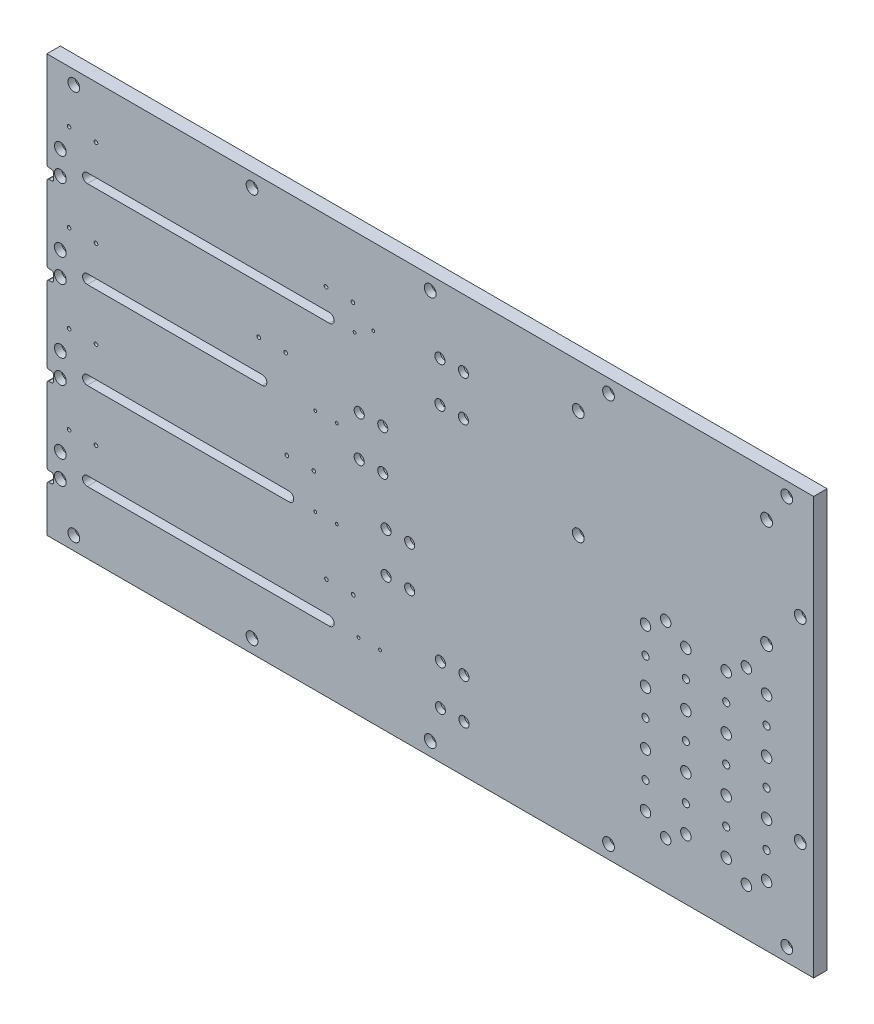
SolidWorks part; units mm, degrees
ref_plane "Front Plane" through (0, 0, 0) normal (0, 0, 1) x (1, 0, 0)
ref_plane "Top Plane" through (0, 0, 0) normal (0, 1, 0) x (1, 0, 0)
ref_plane "Right Plane" through (0, 0, 0) normal (1, 0, 0) x (0, 0, -1)
sketch "Sketch1" plane through (0, 0, 0) normal (0, 0, 1) x (1, 0, 0)
  line L1 (0, 0) -> (723.9, 0)
  line L2 (0, 0) -> (0, -393.7)
  line L3 (0, -393.7) -> (723.9, -393.7)
  line L4 (723.9, 0) -> (723.9, -393.7)
  dimension "D1" = 393.7
  dimension "D2" = 723.9
extrude "Boss-Extrude1" add sketch "Sketch1" against normal blind 12.7
sketch "Sketch2" plane through (0, 0, 0) normal (0, 0, 1) x (1, 0, 0)
  line L0 (38.1, -82.55) -> (266.7, -82.55) construction
  line L1 (38.1, -78.105) -> (266.7, -78.105)
  line L2 (38.1, -86.995) -> (266.7, -86.995)
  line L3 (0, 0) -> (0, -393.7) construction
  line L4 (38.1, -165.1) -> (203.2, -165.1) construction
  line L5 (38.1, -160.655) -> (203.2, -160.655)
  line L6 (38.1, -169.545) -> (203.2, -169.545)
  line L7 (38.1, -247.65) -> (228.6, -247.65) construction
  line L8 (38.1, -243.205) -> (228.6, -243.205)
  line L9 (38.1, -252.095) -> (228.6, -252.095)
  line L10 (38.1, -330.2) -> (266.7, -330.2) construction
  line L11 (38.1, -325.755) -> (266.7, -325.755)
  line L12 (38.1, -334.645) -> (266.7, -334.645)
  arc A0 (38.1, -78.105) -> (38.1, -86.995) centre (38.1, -82.55) ccw
  arc A1 (266.7, -86.995) -> (266.7, -78.105) centre (266.7, -82.55) ccw
  arc A2 (38.1, -160.655) -> (38.1, -169.545) centre (38.1, -165.1) ccw
  arc A3 (203.2, -169.545) -> (203.2, -160.655) centre (203.2, -165.1) ccw
  arc A4 (38.1, -243.205) -> (38.1, -252.095) centre (38.1, -247.65) ccw
  arc A5 (228.6, -252.095) -> (228.6, -243.205) centre (228.6, -247.65) ccw
  arc A6 (38.1, -325.755) -> (38.1, -334.645) centre (38.1, -330.2) ccw
  arc A7 (266.7, -334.645) -> (266.7, -325.755) centre (266.7, -330.2) ccw
  point P2 (152.4, -82.55)
  point P12 (120.65, -165.1)
  point P19 (133.35, -247.65)
  point P24 (152.4, -330.2)
  dimension "D16" = 38.1
  dimension "D1" = 8.89
  dimension "D2" = 38.1
  dimension "D3" = 228.6
  dimension "D4" = 82.55
  dimension "D5" = 8.89
  dimension "D6" = 38.1
  dimension "D7" = 82.55
  dimension "D8" = 165.1
  dimension "D9" = 8.89
  dimension "D10" = 190.5
  dimension "D11" = 82.55
  dimension "D12" = 8.89
  dimension "D13" = 38.1
  dimension "D14" = 82.55
  dimension "D15" = 228.6
extrude "Cut-Extrude1" cut sketch "Sketch2" against normal blind 12.7
ref_plane "Plane1" through (0, -82.55, 0) normal (0, -1, 0) x (-1, 0, 0)
sketch "Sketch5" plane through (0, 0, 0) normal (0, 0, 1) x (1, 0, 0)
  line L0 (0, 0) -> (0, -393.7) construction
  line L1 (0, -174.775) -> (6.35, -174.775)
  line L2 (0, -174.775) -> (0, -184.3)
  line L3 (0, -184.3) -> (6.35, -184.3)
  line L4 (6.35, -174.775) -> (6.35, -184.3)
  line L5 (7, -171.6) -> (0, -171.6) construction
  line L6 (7, -89.05) -> (0, -89.05) construction
  line L7 (0, -92.225) -> (6.35, -92.225)
  line L8 (0, -92.225) -> (0, -101.75)
  line L9 (0, -101.75) -> (6.35, -101.75)
  line L10 (6.35, -92.225) -> (6.35, -101.75)
  line L11 (7, -254.15) -> (0, -254.15) construction
  line L12 (0, -257.325) -> (6.35, -257.325)
  line L13 (0, -257.325) -> (0, -266.85)
  line L14 (0, -266.85) -> (6.35, -266.85)
  line L15 (6.35, -257.325) -> (6.35, -266.85)
  line L16 (7, -336.7) -> (0, -336.7) construction
  line L17 (0, -339.875) -> (6.35, -339.875)
  line L18 (0, -339.875) -> (0, -349.4)
  line L19 (0, -349.4) -> (6.35, -349.4)
  line L20 (6.35, -339.875) -> (6.35, -349.4)
  dimension "D1" = 9.525
  dimension "D2" = 6.35
  dimension "D3" = 3.175
  dimension "D4" = 3.175
  dimension "D5" = 9.525
  dimension "D6" = 6.35
  dimension "D7" = 9.525
  dimension "D8" = 3.175
  dimension "D9" = 6.35
  dimension "D10" = 9.525
  dimension "D11" = 3.175
  dimension "D12" = 6.35
extrude "Cut-Extrude2" cut sketch "Sketch5" against normal through all
sketch "Sketch7" plane through (0, 0, -12.7) normal (0, 0, -1) x (-1, 0, 0)
  circle A6 centre (-20.955, -296.9946) radius 2.0193
  circle A7 centre (-46.355, -296.9946) radius 2.0193
  circle A8 centre (-20.955, -214.3125) radius 2.0193
  circle A9 centre (-46.355, -214.3125) radius 2.0193
  circle A10 centre (-20.955, -131.7625) radius 2.0193
  circle A11 centre (-46.355, -131.7625) radius 2.0193
  point P9 (0, 0)
  point P18 (0, 0)
  point P19 (0, 0)
fillet "Fillet1" radius 2.032 16 edges at (6.35, -101.75, -6.35) (0, -101.75, -6.35) (6.35, -92.225, -6.35) (0, -92.225, -6.35) (6.35, -174.775, -6.35) (0, -174.775, -6.35) (6.35, -184.3, -6.35) (0, -184.3, -6.35) (0, -266.85, -6.35) (6.35, -266.85, -6.35) (0, -257.325, -6.35) (6.35, -257.325, -6.35) (0, -349.4, -6.35) (6.35, -349.4, -6.35) (6.35, -339.875, -6.35) (0, -339.875, -6.35)
hole_wizard "#6-32 Tapped Hole1" positions "Sketch8" profile "Sketch9" tap size "#6-32" standard "ANSI Inch" end condition through all
sketch "Sketch8" plane through (0, 0, -12.7) normal (0, 0, -1) x (-1, 0, 0)
  point P0 (-20.955, -131.7625)
  point P3 (-46.355, -131.7625)
  point P6 (-46.355, -214.3125)
  point P9 (-20.955, -214.3125)
  point P12 (-46.355, -296.9946)
  point P15 (-20.955, -296.9946)
sketch "Sketch9" plane through (20.955, -131.7625, -12.7) normal (1, 0, 0) x (0, 1, 0)
  line L0 (0, 0) -> (0, 12.7)
  line L1 (0, 12.7) -> (1.3525, 12.7)
  line L2 (1.3525, 12.7) -> (1.3525, 0)
  line L5 (1.3525, 0) -> (0, 0)
  line L11 (0, -6.35) -> (0, 107.95) construction
  dimension "Thru Tap Drill Dia." = 2.7051
  dimension "Thru Tap Drill Depth" = 12.7
sketch "Sketch10" plane through (0, 0, 0) normal (0, 0, 1) x (1, 0, 0)
  line L0 (723.9, -393.7) -> (723.9, 0) construction
  line L1 (0, -393.7) -> (723.9, -393.7) construction
  line L2 (0, -351.432) -> (0, -393.7) construction
  line L3 (723.9, -196.85) -> (806.2378, -196.85) construction
  point P0 (698.5, -381)
  point P1 (530.225, -381)
  point P2 (361.95, -381)
  point P3 (193.675, -381)
  point P4 (711.2, -196.85)
  point P7 (25.4, -12.7)
  point P8 (193.675, -12.7)
  point P13 (361.95, -12.7)
  point P14 (530.225, -12.7)
  point P15 (25.4, -381)
  point P18 (698.5, -12.7)
  point P19 (711.2, -288.925)
  point P20 (711.2, -104.775)
  dimension "D1" = 25.4
  dimension "D2" = 12.7
  dimension "D3" = 168.275
  dimension "D4" = 168.275
  dimension "D5" = 168.275
  dimension "D6" = 25.4
  dimension "D7" = 92.075
  dimension "D8" = 92.075
  dimension "D9" = 92.075
  dimension "D10" = 12.7
hole_wizard "CBORE for 1/4 Socket Head Cap Screw1" positions "Sketch13" profile "Sketch14" counterbore size "1/4" standard "ANSI Inch" end condition through all
sketch "Sketch13" plane through (0, 0, 0) normal (0, 0, 1) x (1, 0, 0)
  point P0 (25.4, -381)
  point P3 (193.675, -381)
  point P6 (361.95, -381)
  point P9 (530.225, -381)
  point P12 (698.5, -381)
  point P15 (711.2, -288.925)
  point P21 (711.2, -104.775)
  point P24 (698.5, -12.7)
  point P27 (530.225, -12.7)
  point P30 (361.95, -12.7)
  point P33 (193.675, -12.7)
  point P36 (25.4, -12.7)
sketch "Sketch14" plane through (25.4, -381, 0) normal (1, 0, 0) x (0, -1, 0)
  line L0 (0, 0) -> (0, 12.7)
  line L1 (0, 12.7) -> (3.3782, 12.7)
  line L3 (3.3782, 12.7) -> (3.3782, 6.731)
  line L4 (3.3782, 6.731) -> (5.5562, 6.731)
  line L5 (5.5562, 6.731) -> (5.5562, 0)
  line L7 (5.5562, 0) -> (0, 0)
  line L11 (0, -6.35) -> (0, 107.95) construction
  dimension "Thru Hole Dia." = 6.7564
  dimension "Thru Hole Depth" = 12.7
  dimension "C'Bore Dia." = 11.1125
  dimension "C'Bore Depth" = 6.731
sketch "Sketch15" plane through (0, 0, -12.7) normal (0, 0, -1) x (-1, 0, 0)
  circle A0 centre (-565.15, -184.15) radius 3.9687 construction
  circle A1 centre (-565.15, -184.15) radius 3.9687
  circle A2 centre (-565.15, -209.55) radius 3.175 construction
  circle A3 centre (-565.15, -209.55) radius 3.175
  circle A4 centre (-565.15, -209.55) radius 3.3655
  circle A5 centre (-565.15, -184.15) radius 4.953
  circle A6 centre (-679.45, -336.55) radius 3.9688 construction
  circle A7 centre (-660.4, -349.25) radius 3.9687 construction
  circle A8 centre (-641.35, -336.55) radius 3.9688 construction
  circle A9 centre (-641.35, -311.15) radius 3.175 construction
  circle A10 centre (-679.45, -311.15) radius 3.175 construction
  circle A11 centre (-679.45, -285.75) radius 3.9688 construction
  circle A12 centre (-641.35, -285.75) radius 3.9688 construction
  circle A13 centre (-641.35, -260.35) radius 3.175 construction
  circle A14 centre (-679.45, -260.35) radius 3.175 construction
  circle A15 centre (-679.45, -234.95) radius 3.9688 construction
  circle A16 centre (-641.35, -234.95) radius 3.9688 construction
  circle A17 centre (-679.45, -209.55) radius 3.175 construction
  circle A18 centre (-641.35, -209.55) radius 3.175 construction
  circle A19 centre (-679.45, -184.15) radius 3.9688 construction
  circle A20 centre (-660.4, -171.45) radius 3.9687 construction
  circle A21 centre (-641.35, -184.15) radius 3.9688 construction
  circle A22 centre (-584.2, -171.45) radius 3.9687 construction
  circle A23 centre (-603.25, -184.15) radius 3.9687 construction
  circle A24 centre (-603.25, -209.55) radius 3.175 construction
  circle A25 centre (-603.25, -234.95) radius 3.9687 construction
  circle A26 centre (-603.25, -260.35) radius 3.175 construction
  circle A27 centre (-603.25, -285.75) radius 3.9687 construction
  circle A28 centre (-603.25, -311.15) radius 3.175 construction
  circle A29 centre (-603.25, -336.55) radius 3.9687 construction
  circle A30 centre (-584.2, -349.25) radius 3.9687 construction
  circle A31 centre (-565.15, -336.55) radius 3.9687 construction
  circle A32 centre (-565.15, -311.15) radius 3.175 construction
  circle A33 centre (-565.15, -285.75) radius 3.9687 construction
  circle A34 centre (-565.15, -260.35) radius 3.175 construction
  circle A35 centre (-565.15, -234.95) radius 3.9687 construction
  circle A36 centre (-679.45, -336.55) radius 3.9688
  circle A37 centre (-660.4, -349.25) radius 3.9687
  circle A38 centre (-641.35, -336.55) radius 3.9688
  circle A39 centre (-641.35, -311.15) radius 3.175
  circle A40 centre (-679.45, -311.15) radius 3.175
  circle A41 centre (-679.45, -285.75) radius 3.9688
  circle A42 centre (-641.35, -285.75) radius 3.9688
  circle A43 centre (-641.35, -260.35) radius 3.175
  circle A44 centre (-679.45, -260.35) radius 3.175
  circle A45 centre (-679.45, -234.95) radius 3.9688
  circle A46 centre (-641.35, -234.95) radius 3.9688
  circle A47 centre (-679.45, -209.55) radius 3.175
  circle A48 centre (-641.35, -209.55) radius 3.175
  circle A49 centre (-679.45, -184.15) radius 3.9688
  circle A50 centre (-660.4, -171.45) radius 3.9687
  circle A51 centre (-641.35, -184.15) radius 3.9688
  circle A52 centre (-584.2, -171.45) radius 3.9687
  circle A53 centre (-603.25, -184.15) radius 3.9687
  circle A54 centre (-603.25, -209.55) radius 3.175
  circle A55 centre (-603.25, -234.95) radius 3.9687
  circle A56 centre (-603.25, -260.35) radius 3.175
  circle A57 centre (-603.25, -285.75) radius 3.9687
  circle A58 centre (-603.25, -311.15) radius 3.175
  circle A59 centre (-603.25, -336.55) radius 3.9687
  circle A60 centre (-584.2, -349.25) radius 3.9687
  circle A61 centre (-565.15, -336.55) radius 3.9687
  circle A62 centre (-565.15, -311.15) radius 3.175
  circle A63 centre (-565.15, -285.75) radius 3.9687
  circle A64 centre (-565.15, -260.35) radius 3.175
  circle A65 centre (-565.15, -234.95) radius 3.9687
  circle A66 centre (-565.15, -234.95) radius 4.953
  circle A67 centre (-584.2, -171.45) radius 4.953
  circle A68 centre (-603.25, -184.15) radius 4.953
  circle A69 centre (-603.25, -209.55) radius 3.3655
  circle A70 centre (-603.25, -234.95) radius 4.953
  circle A71 centre (-603.25, -260.35) radius 3.3655
  circle A72 centre (-565.15, -260.35) radius 3.3655
  circle A73 centre (-565.15, -285.75) radius 4.7625
  circle A74 centre (-565.15, -311.15) radius 3.3655
  circle A75 centre (-565.15, -336.55) radius 4.953
  circle A76 centre (-584.2, -349.25) radius 4.953
  circle A77 centre (-603.25, -336.55) radius 4.953
  circle A78 centre (-603.25, -311.15) radius 3.3655
  circle A79 centre (-603.25, -285.75) radius 4.953
  circle A80 centre (-641.35, -184.15) radius 4.953
  circle A81 centre (-641.35, -209.55) radius 3.3655
  circle A82 centre (-641.35, -234.95) radius 4.953
  circle A83 centre (-641.35, -260.35) radius 3.3655
  circle A84 centre (-660.4, -171.45) radius 4.953
  circle A85 centre (-679.45, -184.15) radius 4.953
  circle A86 centre (-679.45, -209.55) radius 3.3655
  circle A87 centre (-679.45, -234.95) radius 4.953
  circle A88 centre (-679.45, -260.35) radius 3.3655
  circle A89 centre (-679.45, -285.75) radius 4.953
  circle A90 centre (-641.35, -285.75) radius 4.953
  circle A91 centre (-641.35, -311.15) radius 3.3655
  circle A92 centre (-679.45, -311.15) radius 3.3655
  circle A93 centre (-679.45, -336.55) radius 4.953
  circle A94 centre (-660.4, -349.25) radius 4.953
  circle A95 centre (-641.35, -336.55) radius 4.953
  dimension "D1" = 6.731
  dimension "D2" = 9.906
  dimension "D3" = 9.906
  dimension "D4" = 9.906
  dimension "D5" = 9.906
  dimension "D6" = 6.731
  dimension "D7" = 9.906
  dimension "D8" = 6.731
  dimension "D9" = 6.731
  dimension "D10" = 9.525
  dimension "D11" = 6.731
  dimension "D12" = 9.906
  dimension "D13" = 9.906
  dimension "D14" = 9.906
  dimension "D15" = 6.731
  dimension "D16" = 9.906
  dimension "D17" = 9.906
  dimension "D18" = 6.731
  dimension "D19" = 9.906
  dimension "D20" = 6.731
  dimension "D21" = 9.906
  dimension "D22" = 9.906
  dimension "D23" = 6.731
  dimension "D24" = 9.906
  dimension "D25" = 6.731
  dimension "D26" = 9.906
  dimension "D27" = 9.906
  dimension "D28" = 6.731
  dimension "D29" = 6.731
  dimension "D30" = 9.906
  dimension "D31" = 9.906
  dimension "D32" = 9.906
extrude "Cut-Extrude9" cut sketch "Sketch15" against normal blind 12.7 from surface at 0
ref_plane "Plane2" through (361.95, 0, 0) normal (1, 0, 0) x (0, 0, -1)
ref_plane "Plane3" through (0, -196.85, 0) normal (0, -1, 0) x (-1, 0, 0)
sketch "Sketch16" plane through (0, 0, 0) normal (0, 0, 1) x (1, 0, 0)
  line L1 (-3.175, -396.875) -> (727.075, -396.875)
  line L2 (-3.175, -396.875) -> (-3.175, 3.175)
  line L3 (-3.175, 3.175) -> (727.075, 3.175)
  line L4 (727.075, -396.875) -> (727.075, 3.175)
  line L5 (-3.175, -396.875) -> (727.075, 3.175) construction
  line L6 (-3.175, 3.175) -> (727.075, -396.875) construction
  line L7 (361.95, -6.985) -> (361.95, 6.985) construction
  line L8 (-6.985, -196.85) -> (6.985, -196.85) construction
  point P0 (361.95, -196.85)
  dimension "D1" = 730.25
  dimension "D2" = 400.05
hole_wizard "CBORE for 1/4 Socket Head Cap Screw2" positions "Sketch17" profile "Sketch18" counterbore size "1/4" standard "ANSI Inch" end condition through all
sketch "Sketch17" plane through (0, 0, 0) normal (0, 0, 1) x (1, 0, 0)
  point P0 (12.7, -319.0875)
  point P3 (12.7, -341.3125)
  point P6 (12.7, -258.7625)
  point P9 (12.7, -236.5375)
  point P12 (12.7, -176.2125)
  point P15 (12.7, -153.9875)
  point P18 (12.7, -93.6625)
  point P21 (12.7, -71.4375)
sketch "Sketch18" plane through (12.7, -319.0875, 0) normal (1, 0, 0) x (0, -1, 0)
  line L0 (0, 0) -> (0, 12.7)
  line L1 (0, 12.7) -> (3.3782, 12.7)
  line L3 (3.3782, 12.7) -> (3.3782, 6.731)
  line L4 (3.3782, 6.731) -> (5.5562, 6.731)
  line L5 (5.5562, 6.731) -> (5.5562, 0)
  line L7 (5.5562, 0) -> (0, 0)
  line L11 (0, -6.35) -> (0, 107.95) construction
  dimension "Thru Hole Dia." = 6.7564
  dimension "Thru Hole Depth" = 12.7
  dimension "C'Bore Dia." = 11.1125
  dimension "C'Bore Depth" = 6.731
hole_wizard "#6-32 Tapped Hole2" positions "Sketch21" profile "Sketch22" tap size "#6-32" standard "ANSI Inch" end condition through all
sketch "Sketch21" plane through (0, 0, 0) normal (0, 0, 1) x (1, 0, 0)
  point P0 (253.365, -247.65)
  point P3 (273.685, -247.65)
  point P6 (253.365, -165.1)
  point P9 (273.685, -165.1)
  point P12 (290.4807, -82.55)
  point P15 (290.4807, -82.55)
  point P17 (308.0783, -72.39)
  point P21 (294.24, -330.2)
  point P24 (314.56, -330.2)
sketch "Sketch22" plane through (253.365, -247.65, 0) normal (1, 0, 0) x (0, -1, 0)
  line L0 (0, 0) -> (0, 12.7)
  line L1 (0, 12.7) -> (1.3525, 12.7)
  line L2 (1.3525, 12.7) -> (1.3525, 0)
  line L5 (1.3525, 0) -> (0, 0)
  line L11 (0, -6.35) -> (0, 107.95) construction
  dimension "Thru Tap Drill Dia." = 2.7051
  dimension "Thru Tap Drill Depth" = 12.7
hole_wizard "CBORE for #10 Socket Head Cap Screw1" positions "Sketch23" profile "Sketch24" counterbore size "#10" standard "ANSI Inch" end condition through all
sketch "Sketch23" plane through (0, 0, 0) normal (0, 0, 1) x (1, 0, 0)
  point P0 (371.075, -101.6)
  point P3 (393.3, -101.6)
  point P6 (393.3, -63.5)
  point P9 (371.075, -63.5)
  point P12 (317.1, -146.05)
  point P15 (294.875, -146.05)
  point P18 (294.875, -184.15)
  point P21 (317.1, -184.15)
  point P24 (320.275, -228.6)
  point P27 (342.5, -228.6)
  point P30 (342.5, -266.7)
  point P33 (320.275, -266.7)
  point P36 (371.5306, -349.25)
  point P39 (393.7556, -349.25)
  point P42 (393.7556, -311.15)
  point P45 (371.5306, -311.15)
sketch "Sketch24" plane through (371.075, -101.6, 0) normal (1, 0, 0) x (0, -1, 0)
  line L0 (0, 0) -> (0, 12.7)
  line L1 (0, 12.7) -> (2.5527, 12.7)
  line L3 (2.5527, 12.7) -> (2.5527, 5.207)
  line L4 (2.5527, 5.207) -> (4.7625, 5.207)
  line L5 (4.7625, 5.207) -> (4.7625, 0)
  line L7 (4.7625, 0) -> (0, 0)
  line L11 (0, -6.35) -> (0, 107.95) construction
  dimension "Thru Hole Dia." = 5.1054
  dimension "Thru Hole Depth" = 12.7
  dimension "C'Bore Dia." = 9.525
  dimension "C'Bore Depth" = 5.207
hole_wizard "#8-32 Tapped Hole1" positions "Sketch26" profile "Sketch27" tap size "#8-32" standard "ANSI Inch" end condition through all
sketch "Sketch26" plane through (0, 0, -12.7) normal (0, 0, -1) x (-1, 0, 0)
  point P0 (-289.2829, -297.6375)
  point P3 (-263.8829, -297.6375)
  point P6 (-226.5885, -215.0875)
  point P9 (-251.9885, -215.0875)
  point P12 (-225.425, -131.7625)
  point P15 (-200.025, -131.7625)
  point P18 (-288.925, -58.7375)
  point P21 (-263.525, -58.7375)
  point P24 (-46.355, -49.2125)
  point P27 (-20.955, -49.2125)
  point P30 (-20.955, -131.7625)
  point P33 (-46.355, -131.7625)
  point P36 (-46.355, -214.3125)
  point P39 (-20.955, -214.3125)
  point P42 (-20.955, -296.9946)
  point P45 (-46.355, -296.9946)
sketch "Sketch27" plane through (289.2829, -297.6375, -12.7) normal (1, 0, 0) x (0, 1, 0)
  line L0 (0, 0) -> (0, 12.7)
  line L1 (0, 12.7) -> (1.7272, 12.7)
  line L2 (1.7272, 12.7) -> (1.7272, 0)
  line L5 (1.7272, 0) -> (0, 0)
  line L11 (0, -6.35) -> (0, 107.95) construction
  dimension "Thru Tap Drill Dia." = 3.4544
  dimension "Thru Tap Drill Depth" = 12.7
cosmetic thread "Hole Thread1" parameters "D2"=4.1656
cosmetic thread "Hole Thread2" parameters "D2"=4.1656
cosmetic thread "Hole Thread3" parameters "D2"=4.1656
cosmetic thread "Hole Thread4" parameters "D2"=4.1656
cosmetic thread "Hole Thread5" parameters "D2"=4.1656
cosmetic thread "Hole Thread6" parameters "D2"=4.1656
cosmetic thread "Hole Thread7" parameters "D2"=4.1656
cosmetic thread "Hole Thread8" parameters "D2"=4.1656
cosmetic thread "Hole Thread9" parameters "D2"=4.1656
cosmetic thread "Hole Thread10" parameters "D2"=4.1656
cosmetic thread "Hole Thread11" parameters "D2"=4.1656
cosmetic thread "Hole Thread12" parameters "D2"=4.1656
cosmetic thread "Hole Thread13" parameters "D2"=4.1656
cosmetic thread "Hole Thread14" parameters "D2"=4.1656
cosmetic thread "Hole Thread15" parameters "D2"=4.1656
cosmetic thread "Hole Thread16" parameters "D2"=4.1656
sketch "Sketch28" plane through (0, 0, -12.7) normal (0, 0, -1) x (-1, 0, 0)
  circle A0 centre (-501.65, -41.275) radius 3.3655 construction
  circle A1 centre (-501.65, -142.875) radius 3.302 construction
  circle A2 centre (-679.45, -142.875) radius 3.3655 construction
  circle A3 centre (-679.45, -41.275) radius 3.3655 construction
  circle A4 centre (-501.65, -41.275) radius 3.3655
  circle A5 centre (-501.65, -142.875) radius 3.302
  circle A6 centre (-679.45, -142.875) radius 3.3655
  circle A7 centre (-679.45, -41.275) radius 3.3655
extrude "Cut-Extrude10" cut sketch "Sketch28" against normal through all
sketch "Sketch29" plane through (0, 0, 0) normal (0, 0, 1) x (1, 0, 0)
  circle A0 centre (679.45, -142.875) radius 5.5626
  circle A1 centre (679.45, -41.275) radius 5.5626
  circle A2 centre (501.65, -41.275) radius 5.5626
  circle A3 centre (501.65, -142.875) radius 5.5626
  dimension "D1" = 11.1252
  dimension "D2" = 11.1252
  dimension "D3" = 11.1252
  dimension "D4" = 11.1252
extrude "Cut-Extrude11" cut sketch "Sketch29" against normal blind 6.731 contours A2 | A3 | A0 | A1
